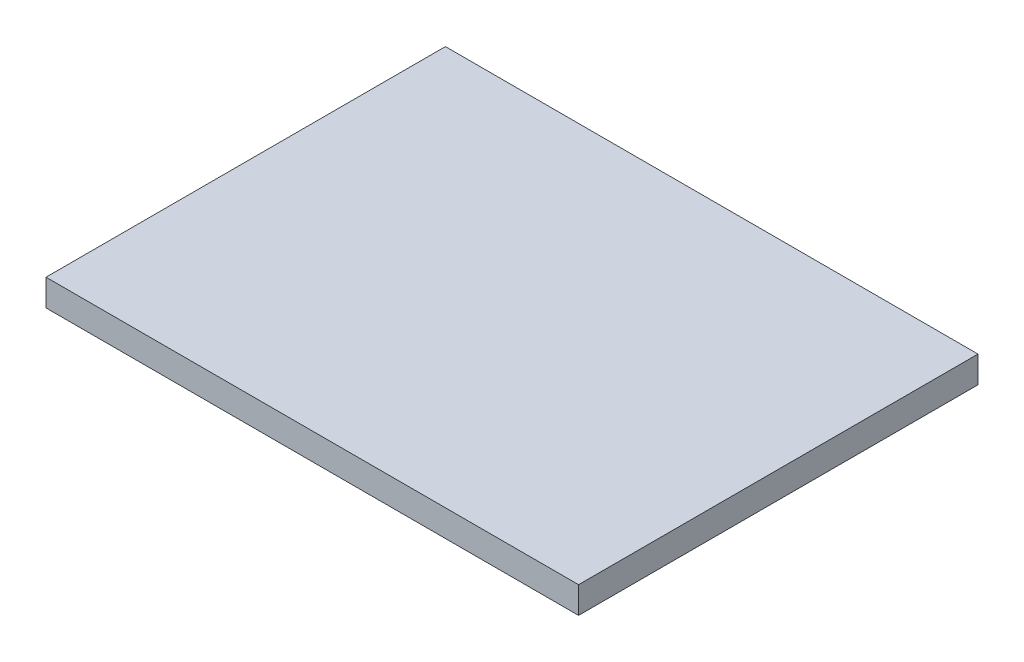
SolidWorks part; units mm, degrees
ref_plane "Front Plane" through (0, 0, 0) normal (0, 0, 1) x (1, 0, 0)
ref_plane "Top Plane" through (0, 0, 0) normal (0, 1, 0) x (1, 0, 0)
ref_plane "Right Plane" through (0, 0, 0) normal (1, 0, 0) x (0, 0, -1)
sketch "Sketch1" plane through (0, 0, 0) normal (0, 1, 0) x (1, 0, 0)
  line L1 (-57.6092, 47.0936) -> (-6.8092, 47.0936)
  line L2 (-57.6092, 47.0936) -> (-57.6092, 8.9936)
  line L3 (-57.6092, 8.9936) -> (-6.8092, 8.9936)
  line L4 (-6.8092, 47.0936) -> (-6.8092, 8.9936)
  line L5 (-57.6092, 47.0936) -> (-6.8092, 8.9936) construction
  line L6 (-57.6092, 8.9936) -> (-6.8092, 47.0936) construction
  point P0 (-32.2092, 28.0436)
extrude "Boss-Extrude1" add sketch "Sketch1" along normal blind 2.54
